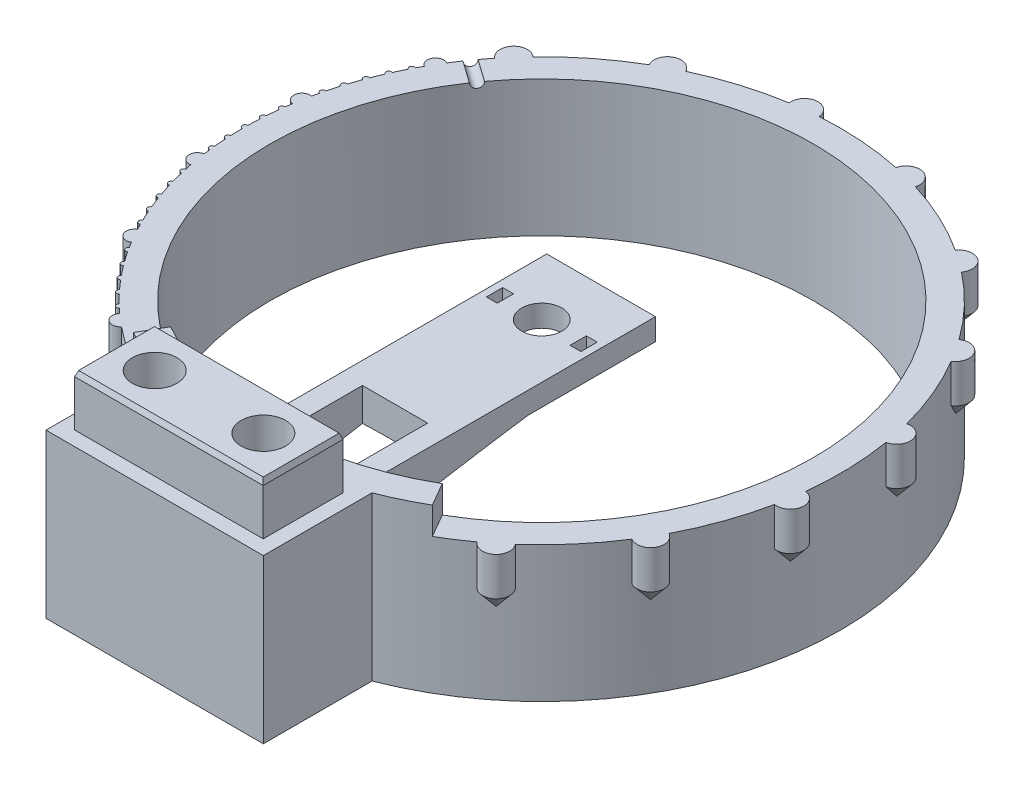
SolidWorks part; units mm, degrees
ref_plane "Спереди" through (0, 0, 0) normal (0, 0, 1) x (1, 0, 0)
ref_plane "Сверху" through (0, 0, 0) normal (0, 1, 0) x (1, 0, 0)
ref_plane "Справа" through (0, 0, 0) normal (1, 0, 0) x (0, 0, -1)
sketch "Sketch1" plane through (0, 0, 0) normal (0, 1, 0) x (1, 0, 0)
  circle A0 centre (0, 0) radius 55
  dimension "D1" = 110
extrude "Boss-Extrude1" add sketch "Sketch1" along normal blind 30
sketch "Sketch6" plane through (0, 30, 0) normal (0, 1, 0) x (1, 0, 0)
  circle A0 centre (0, 0) radius 50
  circle A1 centre (0, 0) radius 55 construction
  dimension "D1" = 5
extrude "Cut-Extrude3" cut sketch "Sketch6" against normal through all
sketch "Sketch7" plane through (0, 30, 0) normal (0, 1, 0) x (1, 0, 0)
  line L0 (0, 0) -> (-27.5, -47.6314) construction
  line L1 (0, 0) -> (27.5, -47.6314) construction
  line L2 (0, 0) -> (0, -50) construction
  line L3 (-27.5, -47.6314) -> (27.5, -47.6314) construction
  line L4 (-25, -43.3013) -> (-27.5, -47.6314)
  line L5 (25, -43.3013) -> (27.5, -47.6314)
  circle A0 centre (0, 0) radius 55 construction
  circle A1 centre (0, 0) radius 50 construction
  arc A2 (-25, -43.3013) -> (25, -43.3013) centre (0, 0) cw
  arc A3 (-27.5, -47.6314) -> (27.5, -47.6314) centre (0, 0) cw
  point P5 (0, -47.6314)
  dimension "D1" = 60
extrude "Cut-Extrude4" cut sketch "Sketch7" against normal blind 5
sketch "Sketch8" plane through (0, 25, 0) normal (0, 1, 0) x (1, 0, 0)
  line L0 (0, 0) -> (0, -38.8668) construction
  line L3 (10, -54.0833) -> (10, 10.9167)
  line L4 (10, 10.9167) -> (-10, 10.9167)
  line L5 (-10, -54.0833) -> (-10, 10.9167)
  line L6 (10, -54.0833) -> (-10, 10.9167) construction
  line L7 (10, 10.9167) -> (-10, -54.0833) construction
  arc A0 (-10, -54.0833) -> (10, -54.0833) centre (0, 0) ccw
  arc A3 (-27.5, -47.6314) -> (27.5, -47.6314) centre (0, 0) ccw construction
  point P3 (0, -21.5833)
  dimension "D1" = 65
  dimension "D2" = 20
extrude "Boss-Extrude3" add sketch "Sketch8" along normal blind 4 from offset 7 offset against normal yes
sketch "Sketch9" plane through (0, 0, 0) normal (0, -1, 0) x (1, 0, 0)
  line L0 (0, -55) -> (0, 55) construction
  line L2 (-20, 51.2348) -> (20, 51.2348)
  line L3 (-20, 51.2348) -> (-20, 71.2348)
  line L4 (-20, 71.2348) -> (20, 71.2348)
  line L5 (20, 51.2348) -> (20, 71.2348)
  line L6 (-20, 51.2348) -> (20, 71.2348) construction
  line L7 (-20, 71.2348) -> (20, 51.2348) construction
  circle A0 centre (0, 0) radius 55 construction
  point P5 (0, 61.2348)
  point P10 (0, 0)
  dimension "D1" = 40
  dimension "D2" = 20
extrude "Boss-Extrude4" add sketch "Sketch9" against normal up to surface (30 mm away) up to face at (0, 30, 48.9832)
sketch "Sketch10" plane through (0, 22, 0) normal (0, 1, 0) x (1, 0, 0)
  line L0 (3.7, 0) -> (10, 0) construction
  line L1 (-3.7, 0) -> (-10, 0) construction
  line L2 (8.7, -1.5) -> (6.7, -1.5)
  line L3 (8.7, -1.5) -> (8.7, 1.5)
  line L4 (8.7, 1.5) -> (6.7, 1.5)
  line L5 (6.7, -1.5) -> (6.7, 1.5)
  line L6 (8.7, -1.5) -> (6.7, 1.5) construction
  line L7 (8.7, 1.5) -> (6.7, -1.5) construction
  line L9 (-6.7, -1.5) -> (-8.7, -1.5)
  line L10 (-6.7, -1.5) -> (-6.7, 1.5)
  line L11 (-6.7, 1.5) -> (-8.7, 1.5)
  line L12 (-8.7, -1.5) -> (-8.7, 1.5)
  line L13 (-6.7, -1.5) -> (-8.7, 1.5) construction
  line L14 (-6.7, 1.5) -> (-8.7, -1.5) construction
  circle A0 centre (0, 0) radius 10 construction
  circle A1 centre (0, 0) radius 3.7
  point P6 (7.7, 0)
  point P13 (-7.7, 0)
  point P18 (-8.0111, 0)
  dimension "D1" = 20
  dimension "D2" = 7.4
  dimension "D3" = 4
  dimension "D4" = 3
  dimension "D5" = 2
  dimension "D6" = 4
extrude "Cut-Extrude5" cut sketch "Sketch10" against normal through all
chamfer "Chamfer2" distance 6 angle 80 1 edges at (0, 18, 50)
sketch "Sketch11" plane through (0, 30, 0) normal (0, 1, 0) x (1, 0, 0)
  line L0 (-20, -61.2348) -> (20, -61.2348) construction
  line L1 (-20, -71.2348) -> (-20, -51.2348) construction
  line L2 (20, -51.2348) -> (20, -71.2348) construction
  circle A0 centre (-10, -61.2348) radius 4.1
  circle A1 centre (10, -61.2348) radius 4.1
  point P10 (0, -61.2348)
  dimension "D1" = 8.2
  dimension "D2" = 20
  dimension "D3" = 10
extrude "Cut-Extrude6" cut sketch "Sketch11" against normal through all
sketch "Sketch12" plane through (0, 25, 0) normal (0, 1, 0) x (1, 0, 0)
  circle A1 centre (-35.6698, -41.8648) radius 1.5
  arc A2 (27.5, -47.6314) -> (-27.5, -47.6314) centre (0, 0) ccw construction
  circle A3 centre (-47.8373, -27.1402) radius 1.5
  circle A4 centre (-54.2349, -9.1422) radius 1.5
  circle A5 centre (-54.0909, 9.9586) radius 1.5
  circle A6 centre (-47.4228, 27.8582) radius 1.5
  circle A7 centre (-35.6698, -41.8648) radius 0.5 construction
  circle A8 centre (-38.0437, -39.72) radius 0.5
  circle A9 centre (-40.2889, -37.4407) radius 0.5
  circle A10 centre (-42.3977, -35.0348) radius 0.5
  circle A11 centre (-44.3631, -32.5103) radius 0.5
  circle A12 centre (-46.1783, -29.8758) radius 0.5
  circle A13 centre (-47.8373, -27.1402) radius 0.5 construction
  circle A14 centre (-49.3344, -24.3128) radius 0.5
  circle A15 centre (-50.6646, -21.4032) radius 0.5
  circle A16 centre (-51.8234, -18.4211) radius 0.5
  circle A17 centre (-52.8068, -15.3766) radius 0.5
  circle A18 centre (-53.6115, -12.2802) radius 0.5
  circle A19 centre (-54.2349, -9.1422) radius 0.5 construction
  circle A20 centre (-54.6747, -5.9732) radius 0.5
  circle A21 centre (-54.9295, -2.7841) radius 0.5
  circle A22 centre (-54.9984, 0.4145) radius 0.5
  circle A23 centre (-54.8813, 3.6117) radius 0.5
  circle A24 centre (-54.5784, 6.7966) radius 0.5
  circle A25 centre (-54.0909, 9.9586) radius 0.5 construction
  circle A26 centre (-53.4204, 13.0869) radius 0.5
  circle A27 centre (-52.569, 16.1708) radius 0.5
  circle A28 centre (-51.5399, 19.2001) radius 0.5
  circle A29 centre (-50.3363, 22.1644) radius 0.5
  circle A30 centre (-48.9624, 25.0537) radius 0.5
  circle A31 centre (-47.4228, 27.8582) radius 0.5 construction
  circle A32 centre (-41.3835, 36.2271) radius 2.5
  circle A33 centre (-25.5578, 48.7011) radius 2.5
  circle A34 centre (-6.3014, 54.6378) radius 2.5
  circle A35 centre (13.8008, 53.2404) radius 2.5
  circle A36 centre (32.0506, 44.6963) radius 2.5
  circle A37 centre (45.9981, 30.1526) radius 2.5
  circle A38 centre (53.7711, 11.5614) radius 2.5
  circle A39 centre (54.3264, -8.5817) radius 2.5
  circle A40 centre (47.5892, -27.5729) radius 2.5
  circle A41 centre (34.4641, -42.8629) radius 2.5
  point P16 (0, 0)
  point P67 (0, 0)
  point P87 (0, 0)
  dimension "D2" = 3
  dimension "D4" = 1
  dimension "D6" = 5
  dimension "D1" = 10
  dimension "D5" = 25
  dimension "D7" = 85
  dimension "D3" = 5
  dimension "D8" = 10
extrude "Boss-Extrude5" add sketch "Sketch12" against normal blind 10
sketch "Sketch13" plane through (0, 25, 0) normal (0, 1, 0) x (1, 0, 0)
  line L0 (-44.8907, 31.7778) -> (0, 0) construction
  line L1 (-38.0434, 25.7054) -> (-46.2053, 31.4832)
  line L2 (-38.0434, 25.7054) -> (-37.4656, 26.5216)
  line L3 (-46.2053, 31.4832) -> (-45.6275, 32.2994)
  line L4 (-37.4656, 26.5216) -> (-45.6275, 32.2994)
  line L5 (-45.9164, 31.8913) -> (-37.7545, 26.1135) construction
  line L6 (-42.1243, 28.5943) -> (-41.5466, 29.4105) construction
  arc A0 (-42.987, 34.3091) -> (-46.6455, 29.1411) centre (0, 0) ccw construction
  point P5 (0, 0)
  point P6 (-41.8354, 29.0024)
  point P9 (-44.8907, 31.7778)
  dimension "D1" = 1
  dimension "D2" = 10
revolve "Cut-Revolve1" cut sketch "Sketch13" angle 360 about L0
sketch "Sketch14" plane through (0, 22, 0) normal (0, 1, 0) x (1, 0, 0)
  line L0 (0, 10.9167) -> (0, -50) construction
  line L1 (10, 10.9167) -> (-10, 10.9167) construction
  line L3 (-6, -27) -> (6, -27)
  line L4 (-6, -27) -> (-6, -47)
  line L5 (-6, -47) -> (6, -47)
  line L6 (6, -27) -> (6, -47)
  line L7 (-6, -27) -> (6, -47) construction
  line L8 (-6, -47) -> (6, -27) construction
  arc A0 (-10, -48.9898) -> (10, -48.9898) centre (0, 0) ccw construction
  point P7 (0, -37)
  dimension "D1" = 20
  dimension "D2" = 12
  dimension "D3" = 13
extrude "Cut-Extrude7" cut sketch "Sketch14" against normal through all
sketch "Sketch15" plane through (0, 30, 0) normal (0, 1, 0) x (1, 0, 0)
  line L0 (19.9782, -61.2348) -> (-20.0306, -61.2348) construction
  line L4 (17.3238, -68.5848) -> (-17.3762, -68.5848)
  line L5 (17.3238, -68.5848) -> (17.3238, -53.8848)
  line L6 (17.3238, -53.8848) -> (-17.3762, -53.8848)
  line L7 (-17.3762, -68.5848) -> (-17.3762, -53.8848)
  line L8 (17.3238, -68.5848) -> (-17.3762, -53.8848) construction
  line L9 (17.3238, -53.8848) -> (-17.3762, -68.5848) construction
  circle A0 centre (-10, -61.2348) radius 4.1
  circle A1 centre (10, -61.2348) radius 4.1
  point P6 (-0.0262, -61.2348)
  point P17 (-10, -61.2348)
  dimension "D1" = 14.7
  dimension "D2" = 34.7
extrude "Boss-Extrude6" add sketch "Sketch15" along normal blind 9.5
chamfer "Chamfer3" distance 1 angle 20 4 edges at (17.3238, 39.5, 61.2348) (-0.0262, 39.5, 68.5848) (-17.3762, 39.5, 61.2348) (-0.0262, 39.5, 53.8848)
sketch "Sketch16" plane through (0, 0, 0) normal (0, -1, 0) x (1, 0, 0)
  line L0 (-20, 61.2348) -> (20, 61.2348) construction
  line L1 (-20, 71.2348) -> (-20, 51.2348) construction
  line L2 (20, 51.2348) -> (20, 71.2348) construction
  line L4 (-17.5, 68.7348) -> (17.5, 68.7348)
  line L5 (-17.5, 68.7348) -> (-17.5, 53.7348)
  line L6 (-17.5, 53.7348) -> (17.5, 53.7348)
  line L7 (17.5, 68.7348) -> (17.5, 53.7348)
  line L8 (-17.5, 68.7348) -> (17.5, 53.7348) construction
  line L9 (-17.5, 53.7348) -> (17.5, 68.7348) construction
  point P6 (0, 61.2348)
  dimension "D1" = 15
  dimension "D2" = 35
extrude "Cut-Extrude8" cut sketch "Sketch16" against normal blind 10
chamfer "Chamfer4" distance 1 angle 70 4 edges at (17.5, 0, 61.2348) (0, 0, 68.7348) (-17.5, 0, 61.2348) (0, 0, 53.7348)
chamfer "Chamfer5" distance 2.45 angle 50 10 edges at (-26.7196, 15, -50.9148) (36.0306, 15, 44.8112) (49.7524, 15, 28.8262) (56.7957, 15, 8.9718) (56.2153, 15, -12.0869) (48.0889, 15, -31.5232) (-43.2646, 15, -37.8738) (33.5074, 15, -46.728) (14.4281, 15, -55.6604) (-6.5879, 15, -57.1214)
